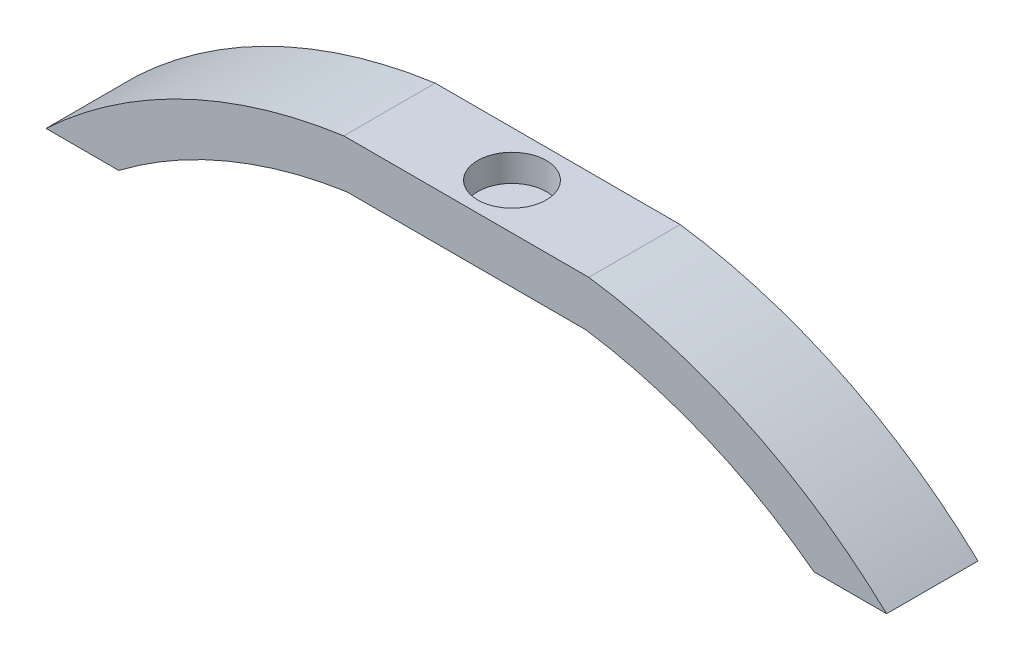
SolidWorks part; units mm, degrees
material "6061 Alloy"
ref_plane "Front Plane" through (0, 0, 0) normal (0, 0, 1) x (1, 0, 0)
ref_plane "Top Plane" through (0, 0, 0) normal (0, 1, 0) x (1, 0, 0)
ref_plane "Right Plane" through (0, 0, 0) normal (1, 0, 0) x (0, 0, -1)
sketch "Sketch1" plane through (0, 0, 0) normal (0, 0, 1) x (1, 0, 0)
  line L0 (-5.2699, 0) -> (5.2699, 0) construction
  line L1 (-13.62, 59.9917) -> (13.62, 59.9917)
  line L3 (-46.735, 44.1517) -> (46.735, 44.1517) construction
  line L4 (-13.2503, 54.7717) -> (13.2503, 54.7717)
  line L5 (-46.735, 44.1517) -> (-38.6503, 44.1517)
  line L6 (46.735, 44.1517) -> (38.6503, 44.1517)
  arc A0 (-13.62, 59.9917) -> (-46.735, 44.1517) centre (-5.2699, 0) ccw
  arc A1 (46.735, 44.1517) -> (13.62, 59.9917) centre (5.2699, 0) ccw
  arc A2 (38.6503, 44.1517) -> (13.2503, 54.7717) centre (5.2699, 0) ccw
  arc A3 (-13.2503, 54.7717) -> (-38.6503, 44.1517) centre (-5.2699, 0) ccw
  arc A4 (43.1615, 40.3466) -> (13.2503, 54.7717) centre (5.2699, 0) ccw construction
  arc A5 (-13.2503, 54.7717) -> (-43.1615, 40.3466) centre (-5.2699, 0) ccw construction
  point P3 (0, 0)
  point P6 (0, 59.9917)
  dimension "D1" = 60.57
  dimension "D2" = 93.47
  dimension "D3" = 27.24
  dimension "D4" = 15.84
  dimension "D5" = 5.22
extrude "Boss-Extrude1" add sketch "Sketch1" along normal blind 10.16
sketch "Sketch2" plane through (0, 59.9917, 0) normal (0, 1, 0) x (1, 0, 0)
  circle A0 centre (0, -5.08) radius 3.81
  dimension "D1" = 7.62
extrude "Cut-Extrude1" cut sketch "Sketch2" against normal blind 3
